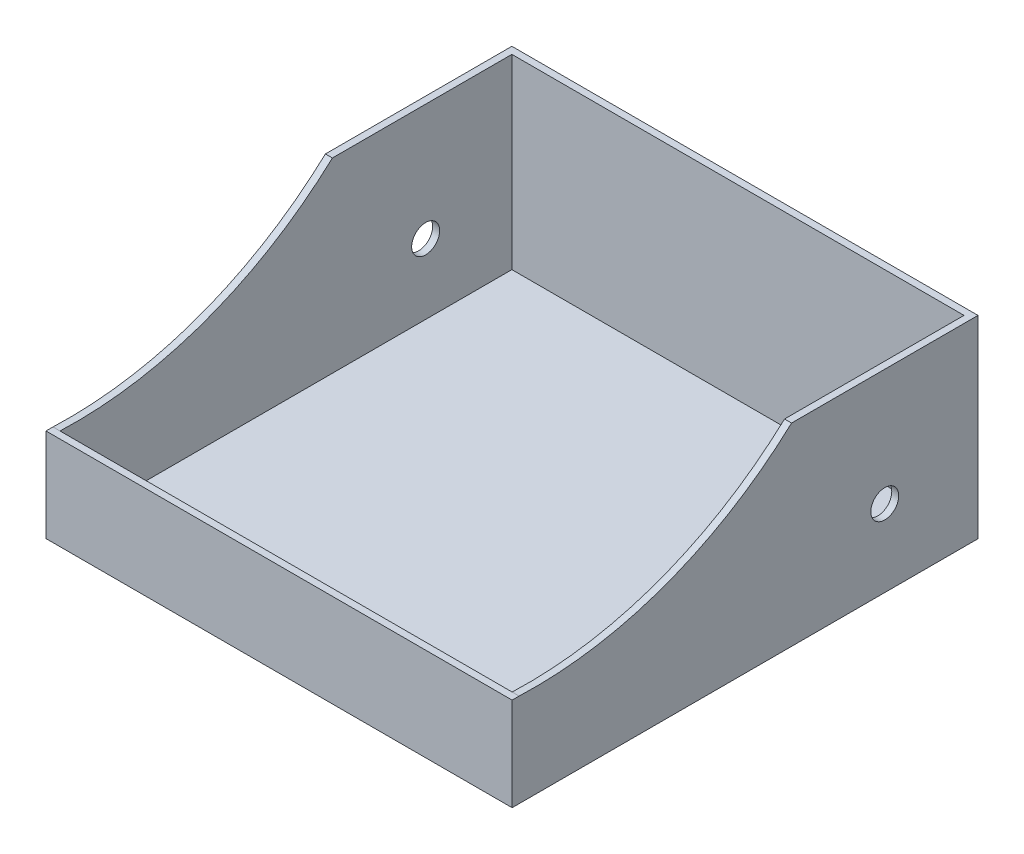
SolidWorks part; units mm, degrees
ref_plane "Front Plane" through (0, 0, 0) normal (0, 0, 1) x (1, 0, 0)
ref_plane "Top Plane" through (0, 0, 0) normal (0, 1, 0) x (1, 0, 0)
ref_plane "Right Plane" through (0, 0, 0) normal (1, 0, 0) x (0, 0, -1)
sketch "Sketch3" plane through (0, 0, 0) normal (0, 1, 0) x (1, 0, 0)
  line L1 (-100, 99.949) -> (100, 99.949)
  line L2 (-100, 99.949) -> (-100, -99.949)
  line L3 (-100, -99.949) -> (100, -99.949)
  line L4 (100, 99.949) -> (100, -99.949)
  line L5 (-100, 99.949) -> (100, -99.949) construction
  line L6 (-100, -99.949) -> (100, 99.949) construction
  point P0 (0, 0)
  dimension "D1" = 200
  dimension "D2" = 199.898
extrude "Boss-Extrude2" add sketch "Sketch3" along normal blind 3
sketch "Sketch9" plane through (0, 3, 0) normal (0, 1, 0) x (1, 0, 0)
  line L0 (-100, 99.949) -> (-100, -99.949) construction
  line L1 (-100, 99.949) -> (-97, 99.949)
  line L2 (-100, 99.949) -> (-100, 19.949)
  line L3 (-100, 19.949) -> (-97, 19.949)
  line L4 (-97, 99.949) -> (-97, 19.949)
  line L5 (100, 99.949) -> (-100, 99.949) construction
  dimension "D1" = 80
  dimension "D2" = 3
extrude "Boss-Extrude3" add sketch "Sketch9" along normal blind 80
sketch "Sketch10" plane through (0, 3, 0) normal (0, 1, 0) x (1, 0, 0)
  line L1 (100, 99.949) -> (97, 99.949)
  line L2 (100, 99.949) -> (100, 19.949)
  line L3 (100, 19.949) -> (97, 19.949)
  line L4 (97, 99.949) -> (97, 19.949)
  dimension "D1" = 3
  dimension "D2" = 80
extrude "Boss-Extrude4" add sketch "Sketch10" along normal blind 80
sketch "Sketch11" plane through (0, 0, 0) normal (0, 1, 0) x (1, 0, 0)
  line L0 (-100, 19.949) -> (-100, -99.949) construction
  line L1 (100, -99.949) -> (-100, -99.949)
  line L2 (100, -99.949) -> (100, -96.949)
  line L3 (100, -96.949) -> (-100, -96.949)
  line L4 (-100, -99.949) -> (-100, -96.949)
  dimension "D1" = 3
extrude "Boss-Extrude6" add sketch "Sketch11" along normal blind 40 contours L3 L4 L1 L2
sketch "Sketch23" plane through (-100, 0, 0) normal (-1, 0, 0) x (0, 0, 1)
  line L0 (-19.949, 3) -> (-99.949, 3)
  line L1 (-99.949, 3) -> (-59.949, 3)
  line L2 (-59.949, 3) -> (-59.949, 33)
  circle A0 centre (-59.949, 33) radius 6
  dimension "D1" = 30
extrude "Cut-Extrude5" cut sketch "Sketch23" against normal blind 228.956 contours A0
sketch "Sketch26" plane through (-100, 0, 0) normal (-1, 0, 0) x (0, 0, 1)
  line L8 (99.949, 0) -> (99.949, 40)
  line L9 (99.949, 40) -> (96.949, 40)
  line L10 (96.949, 40) -> (96.949, 3)
  line L11 (96.949, 3) -> (-19.949, 3)
  line L12 (-19.949, 3) -> (-19.949, 83)
  line L13 (-19.949, 83) -> (-99.949, 83)
  line L14 (-99.949, 83) -> (-99.949, 0)
  line L15 (-99.949, 0) -> (99.949, 0)
  line L16 (99.949, 0) -> (99.949, 40)
  line L17 (99.949, 40) -> (96.949, 40)
  line L21 (-19.949, 83) -> (-99.949, 83)
  line L22 (-99.949, 83) -> (-99.949, 0)
  line L23 (-99.949, 0) -> (99.949, 0)
  arc A0 (-19.949, 83) -> (96.949, 40) centre (90.4056, 202.6084) ccw
  dimension "D1" = 0
extrude "Boss-Extrude8" add sketch "Sketch26" against normal blind 3 contours A0 L17 L16 L23 L22 L21
sketch3d "3DSketch1"
  point P0 (100, 55.9236, -76.3585)
sketch "Sketch29" plane through (100, 0, 0) normal (1, 0, 0) x (0, 0, -1)
  line L4 (-96.949, 3) -> (99.949, 3)
  line L5 (99.949, 3) -> (99.949, 83)
  line L6 (99.949, 83) -> (19.949, 83)
  line L7 (-96.949, 40) -> (-96.949, 3)
  arc A0 (19.949, 83) -> (-96.949, 40) centre (-90.4056, 202.6084) cw
  arc A2 (-96.949, 40) -> (19.949, 83) centre (-90.4056, 202.6084) ccw
  arc A3 (-96.949, 40) -> (19.949, 83) centre (-90.4056, 202.6084) ccw
  line M11 (19.949, 83) -> (19.949, 3)
  line M12 (19.949, 3) -> (-96.949, 3)
  line M13 (-96.949, 3) -> (-96.949, 40)
  dimension "D1" = 0
extrude "Boss-Extrude9" add sketch "Sketch29" against normal blind 3 contours A0 M11 M13 M12
sketch "Sketch30" plane through (100, 0, 0) normal (1, 0, 0) x (0, 0, -1)
  circle A1 centre (59.949, 33) radius 6
  point P1 (0, 0)
extrude "Cut-Extrude6" cut sketch "Sketch30" against normal blind 225.25
sketch "Sketch32" plane through (0, 0, 0) normal (0, 1, 0) x (1, 0, 0)
  line L0 (100, 19.949) -> (100, 99.949) construction
  line L1 (-100, 99.949) -> (100, 99.949)
  line L2 (-100, 99.949) -> (-100, 96.949)
  line L3 (-100, 96.949) -> (100, 96.949)
  line L4 (100, 99.949) -> (100, 96.949)
  point P7 (-244.4928, 29.3699)
  dimension "D1" = 3
extrude "Boss-Extrude12" add sketch "Sketch32" along normal blind 83 contours L3 L4 L1 L2
